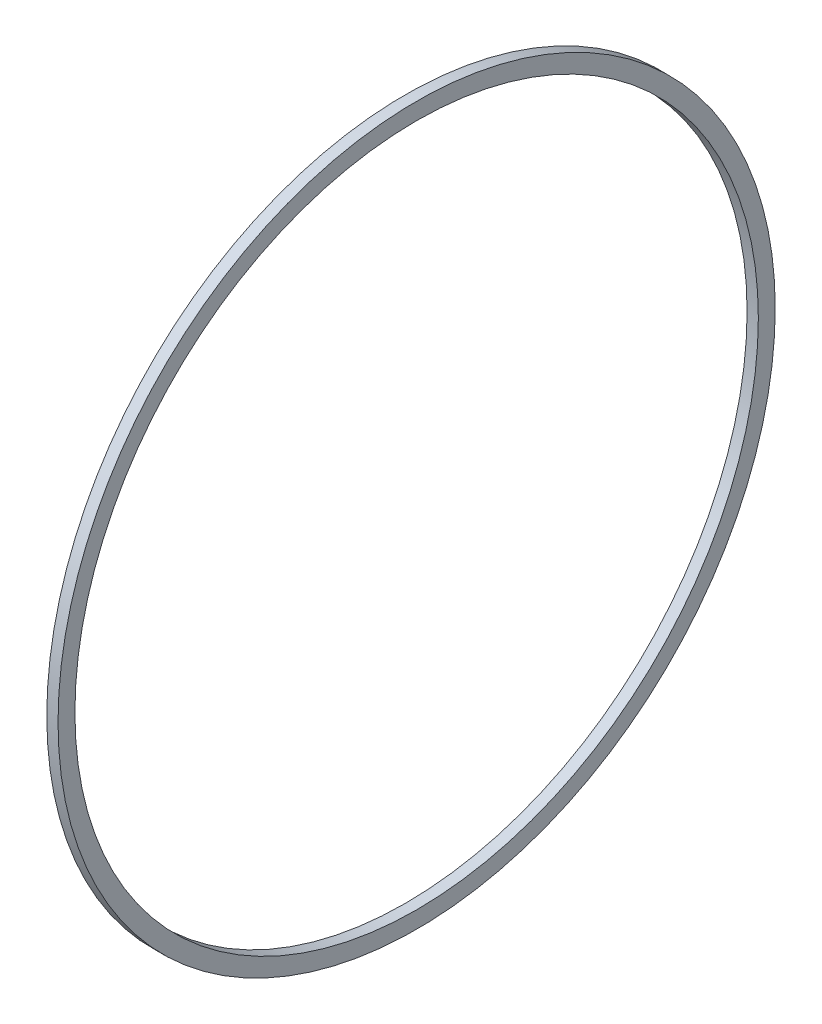
SolidWorks part; units mm, degrees
ref_plane "Front Plane" through (0, 0, 0) normal (0, 0, 1) x (1, 0, 0)
ref_plane "Top Plane" through (0, 0, 0) normal (0, 1, 0) x (1, 0, 0)
ref_plane "Right Plane" through (0, 0, 0) normal (1, 0, 0) x (0, 0, -1)
sketch "Sketch1" plane through (0, 0, 0) normal (1, 0, 0) x (0, 0, -1)
  circle A0 centre (0, 0) radius 63.75
  circle A1 centre (0, 0) radius 60.75
  dimension "D1" = 3
extrude "Boss-Extrude1" add sketch "Sketch1" along normal blind 2
